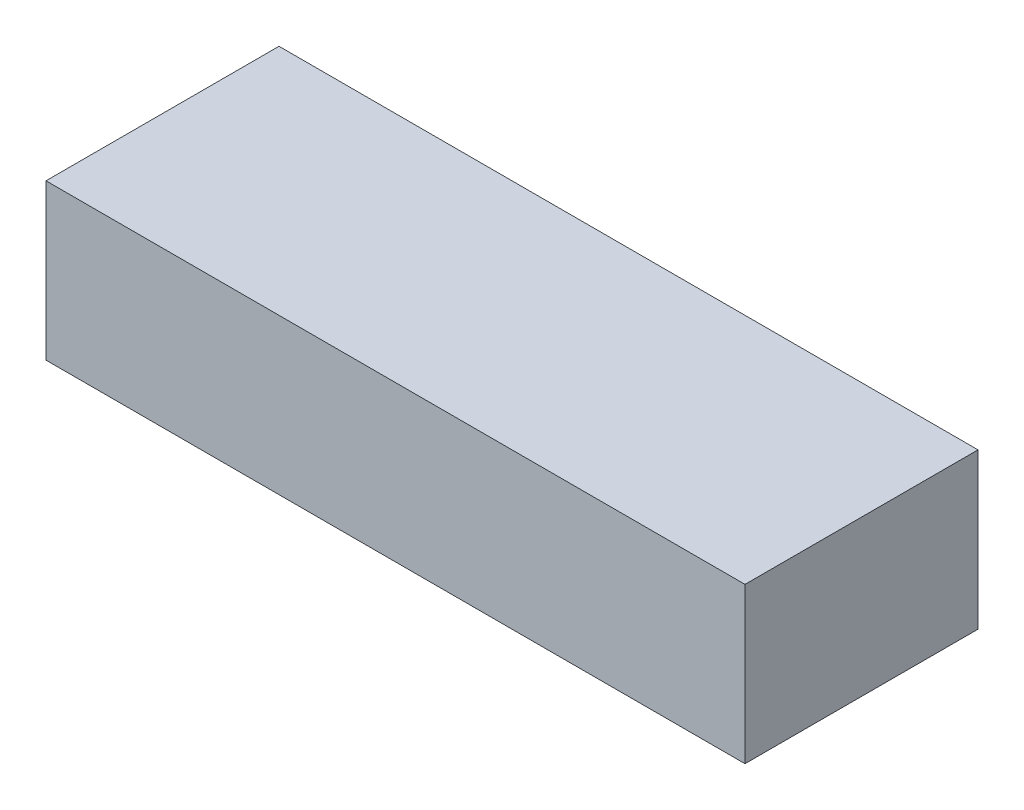
SolidWorks part; units mm, degrees
other "Markup1"
sketch "Sketch2" plane through (90, 20, 0) normal (0.7185, 0.4157, 0.5576) x (0.6707, -0.202, -0.7137)
ref_plane "Front Plane" through (0, 0, 0) normal (0, 0, 1) x (1, 0, 0)
ref_plane "Top Plane" through (0, 0, 0) normal (0, 1, 0) x (1, 0, 0)
ref_plane "Right Plane" through (0, 0, 0) normal (1, 0, 0) x (0, 0, -1)
sketch "Sketch1" plane through (0, 0, 0) normal (0, 1, 0) x (1, 0, 0)
  line L1 (0, 0) -> (90, 0)
  line L2 (0, 0) -> (0, 30)
  line L3 (0, 30) -> (90, 30)
  line L4 (90, 0) -> (90, 30)
  dimension "D1" = 90
  dimension "D2" = 30
extrude "Boss-Extrude1" add sketch "Sketch1" along normal blind 20
